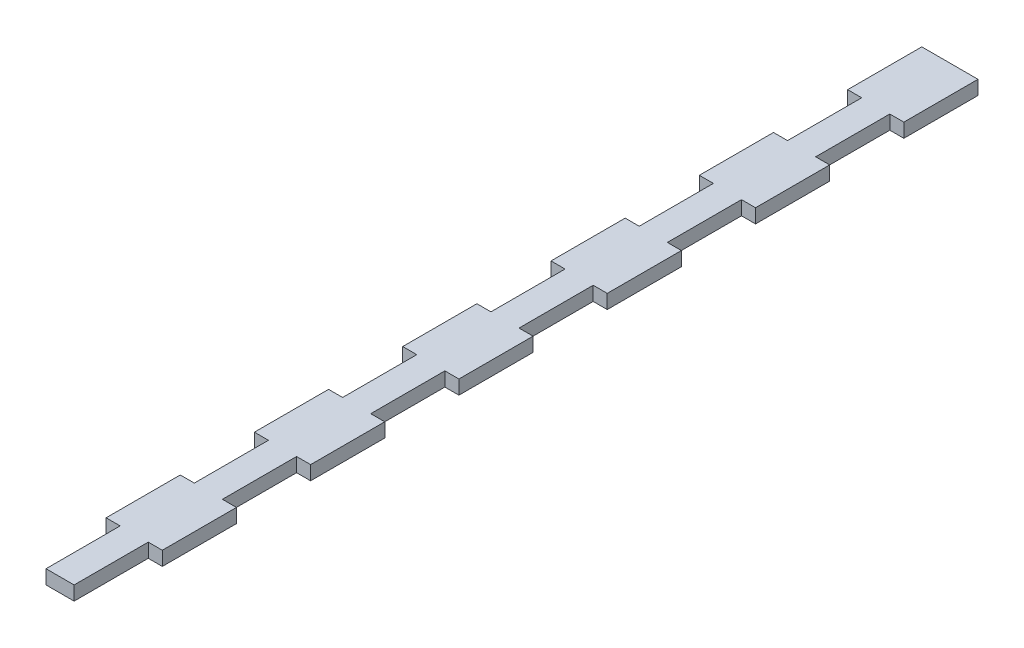
SolidWorks part; units mm, degrees
ref_plane "Front Plane" through (0, 0, 0) normal (0, 0, 1) x (1, 0, 0)
ref_plane "Top Plane" through (0, 0, 0) normal (0, 1, 0) x (1, 0, 0)
ref_plane "Right Plane" through (0, 0, 0) normal (1, 0, 0) x (0, 0, -1)
sketch "Sketch2" plane through (0, 0, 0) normal (0, 1, 0) x (1, 0, 0)
  line L0 (3, 95) -> (3, 79.1667) construction
  line L1 (-6, -95) -> (6, -95)
  line L2 (-6, -95) -> (-6, 95)
  line L3 (-6, 95) -> (6, 95)
  line L4 (6, -95) -> (6, 95)
  line L5 (-6, -95) -> (6, 95) construction
  line L6 (-6, 95) -> (6, -95) construction
  line L7 (3, -79.1667) -> (6, -79.1667)
  line L8 (3, -79.1667) -> (3, -95)
  line L11 (3, -79.1667) -> (6, -95) construction
  line L12 (3, -95) -> (6, -79.1667) construction
  line L13 (3, -47.5) -> (6, -47.5)
  line L14 (3, -47.5) -> (3, -63.3333)
  line L15 (3, -63.3333) -> (6, -63.3333)
  line L17 (3, -47.5) -> (6, -63.3333) construction
  line L18 (3, -63.3333) -> (6, -47.5) construction
  line L19 (3, -15.8333) -> (6, -15.8333)
  line L20 (3, -15.8333) -> (3, -31.6667)
  line L21 (3, -31.6667) -> (6, -31.6667)
  line L23 (3, -15.8333) -> (6, -31.6667) construction
  line L24 (3, -31.6667) -> (6, -15.8333) construction
  line L25 (3, 15.8333) -> (6, 15.8333)
  line L26 (3, 15.8333) -> (3, 0)
  line L27 (3, 0) -> (6, 0)
  line L29 (3, 15.8333) -> (6, 0) construction
  line L30 (3, 0) -> (6, 15.8333) construction
  line L31 (3, 47.5) -> (6, 47.5)
  line L32 (3, 47.5) -> (3, 31.6667)
  line L33 (3, 31.6667) -> (6, 31.6667)
  line L35 (3, 47.5) -> (6, 31.6667) construction
  line L36 (3, 31.6667) -> (6, 47.5) construction
  line L37 (3, 79.1667) -> (6, 79.1667)
  line L38 (3, 79.1667) -> (3, 63.3333)
  line L39 (3, 63.3333) -> (6, 63.3333)
  line L41 (3, 79.1667) -> (6, 63.3333) construction
  line L42 (3, 63.3333) -> (6, 79.1667) construction
  line L43 (3, 63.3333) -> (3, 47.5) construction
  line L44 (3, 31.6667) -> (3, 15.8333) construction
  line L45 (3, 0) -> (3, -15.8333) construction
  line L46 (3, -31.6667) -> (3, -47.5) construction
  line L47 (3, -63.3333) -> (3, -79.1667) construction
  line L48 (0, -95) -> (0, 95) construction
  line L51 (-3, -79.1667) -> (-6, -79.1667)
  line L52 (-3, -79.1667) -> (-3, -95)
  line L53 (-3, -63.3333) -> (-6, -63.3333)
  line L55 (-3, -47.5) -> (-6, -47.5)
  line L56 (-3, -47.5) -> (-3, -63.3333)
  line L57 (-3, -31.6667) -> (-6, -31.6667)
  line L59 (-3, -15.8333) -> (-6, -15.8333)
  line L60 (-3, -15.8333) -> (-3, -31.6667)
  line L61 (-3, 0) -> (-6, 0)
  line L63 (-3, 15.8333) -> (-6, 15.8333)
  line L64 (-3, 15.8333) -> (-3, 0)
  line L65 (-3, 31.6667) -> (-6, 31.6667)
  line L67 (-3, 47.5) -> (-6, 47.5)
  line L68 (-3, 47.5) -> (-3, 31.6667)
  line L69 (-3, 63.3333) -> (-6, 63.3333)
  line L71 (-3, 79.1667) -> (-6, 79.1667)
  line L72 (-3, 79.1667) -> (-3, 63.3333)
  point P0 (0, 0)
  point P6 (4.5, -87.0833)
  point P7 (4.5, -55.4167)
  point P15 (4.5, -23.75)
  point P20 (4.5, 7.9167)
  point P25 (4.5, 39.5833)
  point P30 (4.5, 71.25)
  dimension "D1" = 12
  dimension "D2" = 190
  dimension "D3" = 3
extrude "Boss-Extrude1" add sketch "Sketch2" along normal blind 3 contours L71 L72 L69 L2 L67 L68 L65 L63 L64 L61 L59 L60 L57 L55 L56 L53 L51 L52 L1 L8 L7 L4 L15 L14 L13 L21 L20 L19 L27 L26 L25 L33 L32 L31 L39 L38 L37 L3
sketch "Sketch3" plane through (0, 3, 0) normal (0, 1, 0) x (1, 0, 0)
  line L0 (1, 35.5833) -> (-1, 35.5833)
  line L1 (-1, 35.5833) -> (-1, 27.6667)
  line L2 (-1, 27.6667) -> (2, 27.6667)
  line L3 (2, 27.6667) -> (2, 19.8333)
  line L4 (2, 19.8333) -> (-1, 19.8333)
  line L5 (-1, 19.8333) -> (-1, 11.9167)
  line L6 (-1, 11.9167) -> (1, 11.9167)
  line L7 (1, 11.9167) -> (1, 19.8333)
  line L8 (1, 19.8333) -> (-2, 19.8333)
  line L9 (-2, 19.8333) -> (-2, 27.6667)
  line L10 (-2, 27.6667) -> (1, 27.6667)
  line L11 (1, 27.6667) -> (1, 35.5833)
  line L12 (2, 23.75) -> (6, 23.75) construction
  line L13 (6, 15.8333) -> (6, 31.6667) construction
  line L14 (-1, 35.5833) -> (3, 35.5833) construction
  line L15 (3, 47.5) -> (3, 31.6667) construction
  line L16 (4.5, 31.6667) -> (4.5, 27.6667) construction
  line L17 (3, 31.6667) -> (6, 31.6667) construction
  line L18 (0, 35.5833) -> (0, 39.5833) construction
  line L19 (1, -4) -> (1, 3.9167)
  line L20 (1, 3.9167) -> (-1, 3.9167)
  line L21 (-1, 3.9167) -> (-1, -4)
  line L22 (-1, -4) -> (2, -4)
  line L23 (2, -4) -> (2, -11.8333)
  line L24 (2, -11.8333) -> (-1, -11.8333)
  line L25 (-1, -11.8333) -> (-1, -19.75)
  line L26 (-1, -19.75) -> (1, -19.75)
  line L27 (1, -19.75) -> (1, -11.8333)
  line L28 (1, -11.8333) -> (-2, -11.8333)
  line L29 (-2, -11.8333) -> (-2, -4)
  line L30 (-2, -4) -> (1, -4)
  line L31 (1, -35.6667) -> (1, -27.75)
  line L32 (1, -27.75) -> (-1, -27.75)
  line L33 (-1, -27.75) -> (-1, -35.6667)
  line L34 (-1, -35.6667) -> (2, -35.6667)
  line L35 (2, -35.6667) -> (2, -43.5)
  line L36 (2, -43.5) -> (-1, -43.5)
  line L37 (-1, -43.5) -> (-1, -51.4167)
  line L38 (-1, -51.4167) -> (1, -51.4167)
  line L39 (1, -51.4167) -> (1, -43.5)
  line L40 (1, -43.5) -> (-2, -43.5)
  line L41 (-2, -43.5) -> (-2, -35.6667)
  line L42 (-2, -35.6667) -> (1, -35.6667)
  line L43 (1, -67.3333) -> (1, -59.4167)
  line L44 (1, -59.4167) -> (-1, -59.4167)
  line L45 (-1, -59.4167) -> (-1, -67.3333)
  line L46 (-1, -67.3333) -> (2, -67.3333)
  line L47 (2, -67.3333) -> (2, -75.1667)
  line L48 (2, -75.1667) -> (-1, -75.1667)
  line L49 (-1, -75.1667) -> (-1, -83.0833)
  line L50 (-1, -83.0833) -> (1, -83.0833)
  line L51 (1, -83.0833) -> (1, -75.1667)
  line L52 (1, -75.1667) -> (-2, -75.1667)
  line L53 (-2, -75.1667) -> (-2, -67.3333)
  line L54 (-2, -67.3333) -> (1, -67.3333)
  line L55 (6, -15.8333) -> (6, 0) construction
  line L56 (1, -83.0833) -> (1, -89)
  line L57 (1, -89) -> (-1, -89)
  line L58 (-1, -89) -> (-1, -83.0833)
  line L59 (-3, -95) -> (3, -95) construction
  line L60 (-2, 59.3333) -> (2, 59.3333)
  line L61 (2, 59.3333) -> (2, 51.5)
  line L62 (2, 51.5) -> (-1, 51.5)
  line L63 (-1, 51.5) -> (-1, 43.5833)
  line L64 (-1, 43.5833) -> (1, 43.5833)
  line L65 (1, 43.5833) -> (1, 51.5)
  line L66 (1, 51.5) -> (-2, 51.5)
  line L67 (-2, 51.5) -> (-2, 59.3333)
  line L68 (2, 63.3333) -> (2, 59.3333) construction
  line L69 (-6, 63.3333) -> (-3, 63.3333) construction
  line L70 (6, 59.3333) -> (2, 59.3333) construction
  line L71 (6, 47.5) -> (6, 63.3333) construction
  line L72 (-1, 43.5833) -> (3, 43.5833) construction
  line L73 (0, 39.5833) -> (0, 43.5833) construction
  line L74 (4.5, 47.5) -> (4.5, 51.5) construction
  line L75 (3, 47.5) -> (6, 47.5) construction
  point P2 (0, 11.9167)
  point P18 (6, 23.75)
  point P28 (3, 39.5833)
  point P29 (2, -7.9167)
  point P68 (6, -7.9167)
  point P82 (0, 59.3333)
  dimension "D1" = 4
  dimension "D3" = 6
  dimension "D2" = 4
